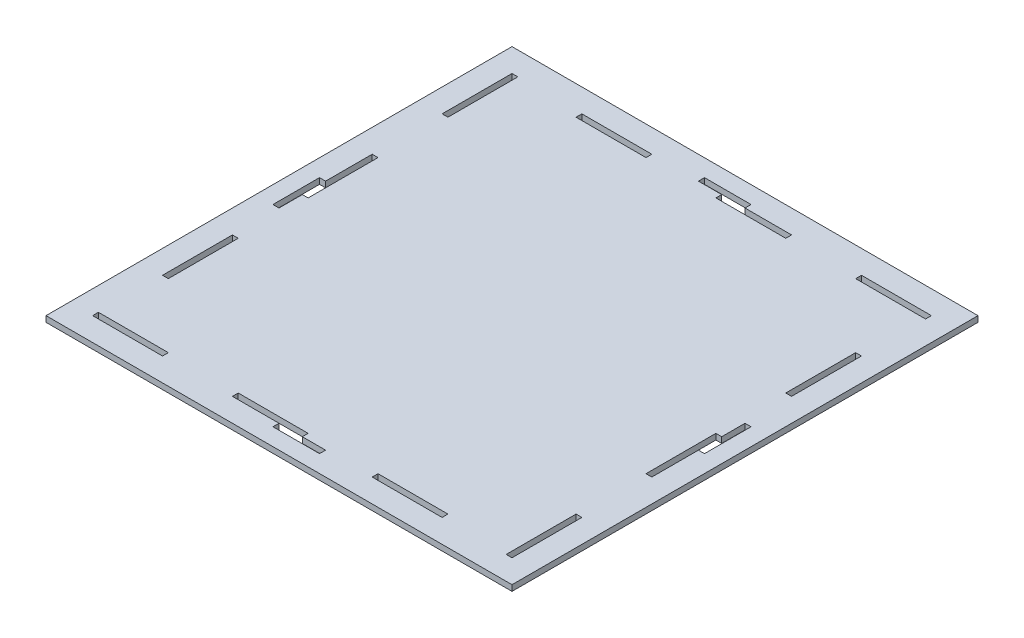
SolidWorks part; units mm, degrees
material "Acrylic (Medium-high impact)"
ref_plane "Front Plane" through (0, 0, 0) normal (0, 0, 1) x (1, 0, 0)
ref_plane "Top Plane" through (0, 0, 0) normal (0, 1, 0) x (1, 0, 0)
ref_plane "Right Plane" through (0, 0, 0) normal (1, 0, 0) x (0, 0, -1)
sketch "Sketch1" plane through (0, 0, 0) normal (0, 1, 0) x (1, 0, 0)
  line L0 (-76.2, 114.3) -> (-76.2, 111.125)
  line L1 (-114.3, 114.3) -> (114.3, 114.3)
  line L2 (-114.3, 114.3) -> (-114.3, -114.3)
  line L3 (-114.3, -114.3) -> (114.3, -114.3)
  line L4 (114.3, 114.3) -> (114.3, -114.3)
  line L5 (-114.3, 114.3) -> (-76.2, 114.3)
  line L6 (-114.3, 114.3) -> (-114.3, 111.125)
  line L7 (-114.3, 111.125) -> (-76.2, 111.125)
  line L8 (-76.2, 114.3) -> (-76.2, 111.125)
  line L9 (-76.2, 114.3) -> (-38.1, 114.3)
  line L10 (-38.1, 114.3) -> (-38.1, 111.125)
  line L11 (-76.2, 111.125) -> (-38.1, 111.125)
  line L12 (-38.1, 114.3) -> (-38.1, 111.125)
  line L13 (-38.1, 114.3) -> (0, 114.3)
  line L14 (0, 114.3) -> (0, 111.125)
  line L15 (-38.1, 111.125) -> (0, 111.125)
  line L16 (0, 114.3) -> (0, 111.125)
  line L17 (0, 114.3) -> (38.1, 114.3)
  line L18 (38.1, 114.3) -> (38.1, 111.125)
  line L19 (0, 111.125) -> (38.1, 111.125)
  line L20 (38.1, 114.3) -> (38.1, 111.125)
  line L21 (38.1, 114.3) -> (76.2, 114.3)
  line L22 (76.2, 114.3) -> (76.2, 111.125)
  line L23 (38.1, 111.125) -> (76.2, 111.125)
  line L24 (76.2, 114.3) -> (76.2, 111.125)
  line L25 (76.2, 114.3) -> (114.3, 114.3)
  line L26 (114.3, 114.3) -> (114.3, 111.125)
  line L27 (76.2, 111.125) -> (114.3, 111.125)
  line L76 (-76.2, -114.3) -> (-76.2, -111.125)
  line L77 (-114.3, -114.3) -> (-76.2, -114.3)
  line L78 (-114.3, -114.3) -> (-114.3, -111.125)
  line L79 (-114.3, -111.125) -> (-76.2, -111.125)
  line L80 (-76.2, -114.3) -> (-76.2, -111.125)
  line L81 (-76.2, -114.3) -> (-38.1, -114.3)
  line L82 (-38.1, -114.3) -> (-38.1, -111.125)
  line L83 (-76.2, -111.125) -> (-38.1, -111.125)
  line L84 (-38.1, -114.3) -> (-38.1, -111.125)
  line L85 (-38.1, -114.3) -> (0, -114.3)
  line L86 (0, -114.3) -> (0, -111.125)
  line L87 (-38.1, -111.125) -> (0, -111.125)
  line L88 (0, -114.3) -> (0, -111.125)
  line L89 (0, -114.3) -> (38.1, -114.3)
  line L90 (38.1, -114.3) -> (38.1, -111.125)
  line L91 (0, -111.125) -> (38.1, -111.125)
  line L92 (38.1, -114.3) -> (38.1, -111.125)
  line L93 (38.1, -114.3) -> (76.2, -114.3)
  line L94 (76.2, -114.3) -> (76.2, -111.125)
  line L95 (38.1, -111.125) -> (76.2, -111.125)
  line L96 (76.2, -114.3) -> (76.2, -111.125)
  line L97 (76.2, -114.3) -> (114.3, -114.3)
  line L98 (114.3, -114.3) -> (114.3, -111.125)
  line L99 (76.2, -111.125) -> (114.3, -111.125)
  line L148 (-114.3, 76.2) -> (-114.3, 38.1)
  line L149 (-114.3, 114.3) -> (-111.125, 114.3)
  line L150 (-114.3, 114.3) -> (-114.3, 76.2)
  line L151 (-114.3, 76.2) -> (-111.125, 76.2)
  line L152 (-111.125, 114.3) -> (-111.125, 76.2)
  line L153 (-114.3, 76.2) -> (-111.125, 76.2)
  line L154 (-111.125, 76.2) -> (-111.125, 38.1)
  line L155 (-114.3, 38.1) -> (-111.125, 38.1)
  line L156 (-114.3, 38.1) -> (-114.3, 0)
  line L157 (-114.3, 38.1) -> (-111.125, 38.1)
  line L158 (-111.125, 38.1) -> (-111.125, 0)
  line L159 (-114.3, 0) -> (-111.125, 0)
  line L160 (-114.3, 0) -> (-114.3, -38.1)
  line L161 (-114.3, 0) -> (-111.125, 0)
  line L162 (-111.125, 0) -> (-111.125, -38.1)
  line L163 (-114.3, -38.1) -> (-111.125, -38.1)
  line L164 (-114.3, -38.1) -> (-114.3, -76.2)
  line L165 (-114.3, -38.1) -> (-111.125, -38.1)
  line L166 (-111.125, -38.1) -> (-111.125, -76.2)
  line L167 (-114.3, -76.2) -> (-111.125, -76.2)
  line L168 (-114.3, -76.2) -> (-114.3, -114.3)
  line L169 (-114.3, -76.2) -> (-111.125, -76.2)
  line L170 (-111.125, -76.2) -> (-111.125, -114.3)
  line L171 (-114.3, -114.3) -> (-111.125, -114.3)
  line L220 (111.125, 76.2) -> (111.125, 38.1)
  line L221 (111.125, 114.3) -> (114.3, 114.3)
  line L222 (111.125, 114.3) -> (111.125, 76.2)
  line L223 (111.125, 76.2) -> (114.3, 76.2)
  line L224 (114.3, 114.3) -> (114.3, 76.2)
  line L225 (111.125, 76.2) -> (114.3, 76.2)
  line L226 (114.3, 76.2) -> (114.3, 38.1)
  line L227 (111.125, 38.1) -> (114.3, 38.1)
  line L228 (111.125, 38.1) -> (111.125, 0)
  line L229 (111.125, 38.1) -> (114.3, 38.1)
  line L230 (114.3, 38.1) -> (114.3, 0)
  line L231 (111.125, 0) -> (114.3, 0)
  line L232 (111.125, 0) -> (111.125, -38.1)
  line L233 (111.125, 0) -> (114.3, 0)
  line L234 (114.3, 0) -> (114.3, -38.1)
  line L235 (111.125, -38.1) -> (114.3, -38.1)
  line L236 (111.125, -38.1) -> (111.125, -76.2)
  line L237 (111.125, -38.1) -> (114.3, -38.1)
  line L238 (114.3, -38.1) -> (114.3, -76.2)
  line L239 (111.125, -76.2) -> (114.3, -76.2)
  line L240 (111.125, -76.2) -> (111.125, -114.3)
  line L241 (111.125, -76.2) -> (114.3, -76.2)
  line L242 (114.3, -76.2) -> (114.3, -114.3)
  line L243 (111.125, -114.3) -> (114.3, -114.3)
  line L292 (0, 114.3) -> (0, -114.3) construction
  line L293 (-127, 127) -> (127, 127)
  line L294 (-127, 127) -> (-127, -127)
  line L295 (-127, -127) -> (127, -127)
  line L296 (127, 127) -> (127, -127)
  line L297 (-127, 127) -> (127, -127) construction
  line L298 (-127, -127) -> (127, 127) construction
  line L299 (-12.7, 117.602) -> (12.7, 117.602)
  line L300 (-12.7, 117.602) -> (-12.7, 114.3)
  line L301 (-12.7, 114.3) -> (12.7, 114.3)
  line L302 (12.7, 117.602) -> (12.7, 114.3)
  line L303 (114.3, 12.7) -> (117.602, 12.7)
  line L304 (114.3, 12.7) -> (114.3, -12.7)
  line L305 (114.3, -12.7) -> (117.602, -12.7)
  line L306 (117.602, 12.7) -> (117.602, -12.7)
  line L307 (-12.7, -117.602) -> (12.7, -117.602)
  line L308 (-12.7, -117.602) -> (-12.7, -114.3)
  line L309 (-12.7, -114.3) -> (12.7, -114.3)
  line L310 (12.7, -117.602) -> (12.7, -114.3)
  line L311 (-114.3, -12.7) -> (-117.602, -12.7)
  line L312 (-114.3, -12.7) -> (-114.3, 12.7)
  line L313 (-114.3, 12.7) -> (-117.602, 12.7)
  line L314 (-117.602, -12.7) -> (-117.602, 12.7)
  line L315 (114.3, 0) -> (-114.3, 0) construction
  point P5 (0, 114.3)
  point P7 (-114.3, 0)
  point P32 (0, 0)
  dimension "D1" = 228.6
  dimension "D2" = 228.6
  dimension "D3" = 38.1
  dimension "D4" = 3.175
  dimension "D7" = 38.1
  dimension "D8" = 3.175
  dimension "D11" = 12.7
  dimension "D12" = 3.302
  dimension "D13" = 25.4
  dimension "D5" = 6
  dimension "D6" = 6
  dimension "D9" = 6
  dimension "D10" = 6
extrude "Boss-Extrude1" add sketch "Sketch1" along normal blind 3.175 contours L5 L152 L7 L0 | L10 L15 L14 L1 | L18 L23 L22 L1 | L222 L223 L4 L27 | L228 L231 L4 L227 | L236 L239 L4 L235 | L240 L99 L94 L3 | L91 L86 L3 L90 | L83 L76 L3 L82 | L170 L167 L2 L79 | L2 L163 L162 L159 | L2 L155 L154 L151 | L240 L236 L232 L228 L220 L222 L27 L23 L19 L15 L11 L7 L152 L154 L158 L162 L166 L170 L79 L83 L87 L91 L95 L99 | L296 L293 L294 L295 L311 L314 L313 L2 L1 L5 L300 L299 L302 L17 L25 L4 L303 L306 L305 L234 L97 L3 L89 L310 L307 L308 L77 L160
equation "\"D7@Sketch1\"=\"D1@Sketch1\"/\"D5@Sketch1\""
equation "\"D3@Sketch1\"=\"D2@Sketch1\"/\"D9@Sketch1\""
